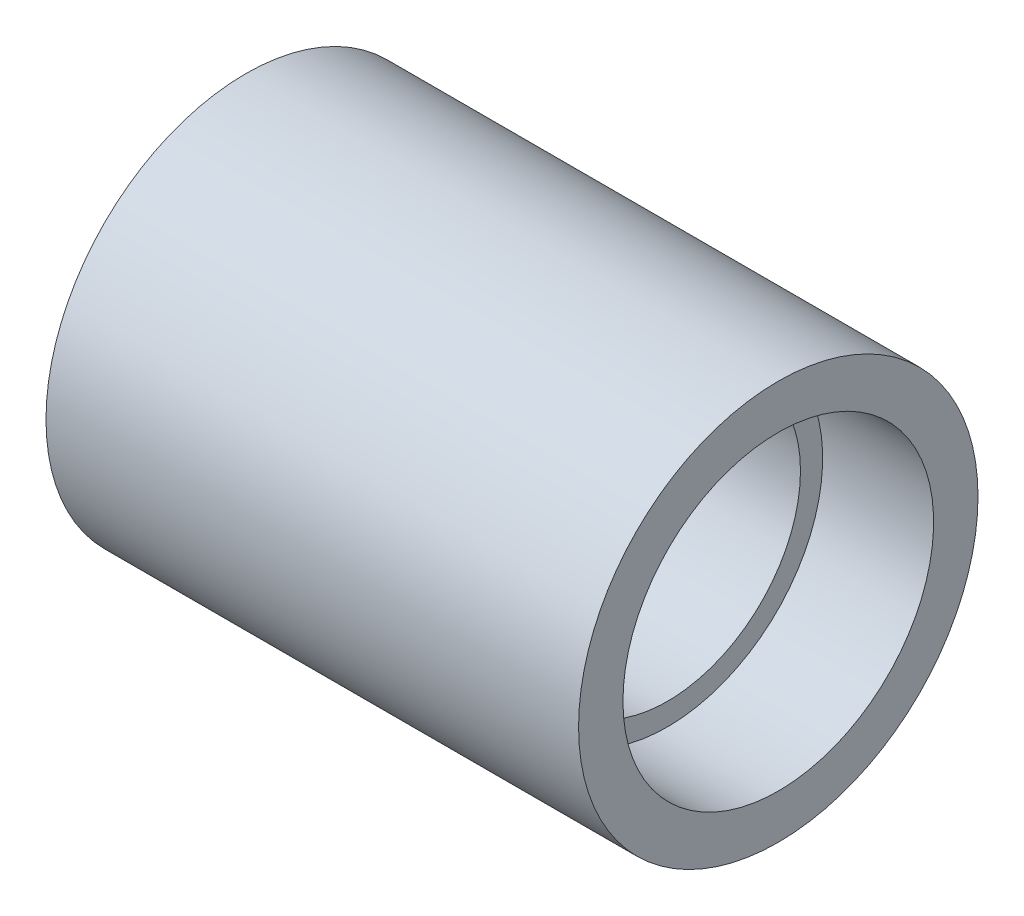
SolidWorks part; units mm, degrees
material "2014-T6"
ref_plane "Ebene vorne" through (0, 0, 0) normal (0, 0, 1) x (1, 0, 0)
ref_plane "Ebene oben" through (0, 0, 0) normal (0, 1, 0) x (1, 0, 0)
ref_plane "Ebene rechts" through (0, 0, 0) normal (1, 0, 0) x (0, 0, -1)
sketch "Skizze1" plane through (0, 0, 0) normal (0, 0, 1) x (1, 0, 0)
  line L0 (-8.5081, 0) -> (23.545, 0) construction
  line L1 (-6, 4.5) -> (-6, 3.5)
  line L2 (-6, 3.5) -> (-3.5, 3.5)
  line L3 (-3.5, 3.5) -> (-3.5, 3)
  line L4 (-3.5, 3) -> (3.5, 3)
  line L5 (3.5, 3) -> (3.5, 3.5)
  line L6 (3.5, 3.5) -> (6, 3.5)
  line L7 (6, 3.5) -> (6, 4.5)
  line L8 (6, 4.5) -> (-6, 4.5)
  line L9 (0, 3) -> (0, 0) construction
  dimension "D1" = 7
  dimension "D2" = 6
  dimension "D3" = 7
  dimension "D4" = 2.5
  dimension "D5" = 9
revolve "Rotation1" add sketch "Skizze1" angle 360 about L0
